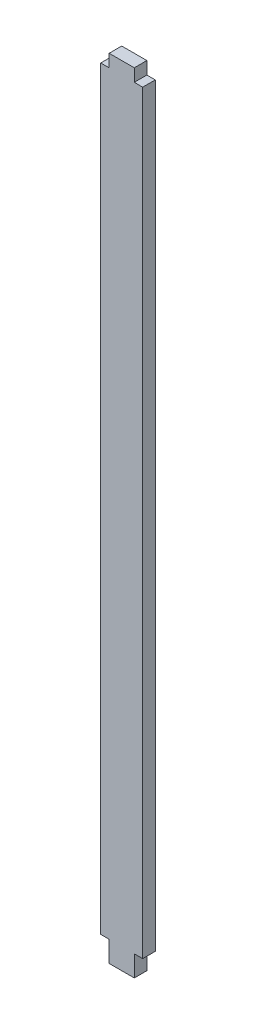
SolidWorks part; units mm, degrees
ref_plane "Plano frontal" through (0, 0, 0) normal (0, 0, 1) x (1, 0, 0)
ref_plane "Plano superior" through (0, 0, 0) normal (0, 1, 0) x (1, 0, 0)
ref_plane "Plano direito" through (0, 0, 0) normal (1, 0, 0) x (0, 0, -1)
sketch "Esboço1" plane through (0, 0, 0) normal (0, 0, 1) x (1, 0, 0)
  line L0 (-3, 90) -> (-5, 90)
  line L1 (5, -90) -> (3, -90)
  line L2 (5, -90) -> (5, 90)
  line L3 (5, 90) -> (3, 90)
  line L4 (-5, -90) -> (-5, 90)
  line L5 (5, -90) -> (-5, 90) construction
  line L6 (5, 90) -> (-5, -90) construction
  line L7 (44.6447, 25) -> (65.3553, 25) construction
  line L8 (-3, -90) -> (-3, -95)
  line L9 (-3, -95) -> (3, -95)
  line L10 (3, -90) -> (3, -95)
  line L11 (-3, -90) -> (-5, -90)
  line L12 (3, 90) -> (3, 93)
  line L13 (3, 93) -> (-3, 93)
  line L14 (-3, 90) -> (-3, 93)
  line L15 (44.6447, 25) -> (65.3553, -25) construction
  line L16 (44.6447, -25) -> (65.3553, 25) construction
  line L17 (37.3223, -17.6777) -> (72.6777, 17.6777) construction
  line L18 (55, 25) -> (55, -25) construction
  line L21 (65.3553, 25) -> (80, 10.3553) construction
  line L22 (80, 10.3553) -> (80, -10.3553) construction
  line L23 (80, -10.3553) -> (65.3553, -25) construction
  line L24 (65.3553, -25) -> (44.6447, -25) construction
  line L25 (44.6447, -25) -> (30, -10.3553) construction
  line L26 (30, -10.3553) -> (30, 10.3553) construction
  line L27 (30, 10.3553) -> (44.6447, 25) construction
  point P0 (0, 0)
  point P14 (0, -95)
  point P15 (0, 93)
  point P19 (30, 0)
  dimension "D1" = 3
  dimension "D2" = 6
  dimension "D3" = 10
  dimension "D4" = 5
  dimension "D5" = 180
  dimension "D6" = 30
  dimension "D7" = 50
extrude "Ressalto-extrusão1" add sketch "Esboço1" along normal blind 3
